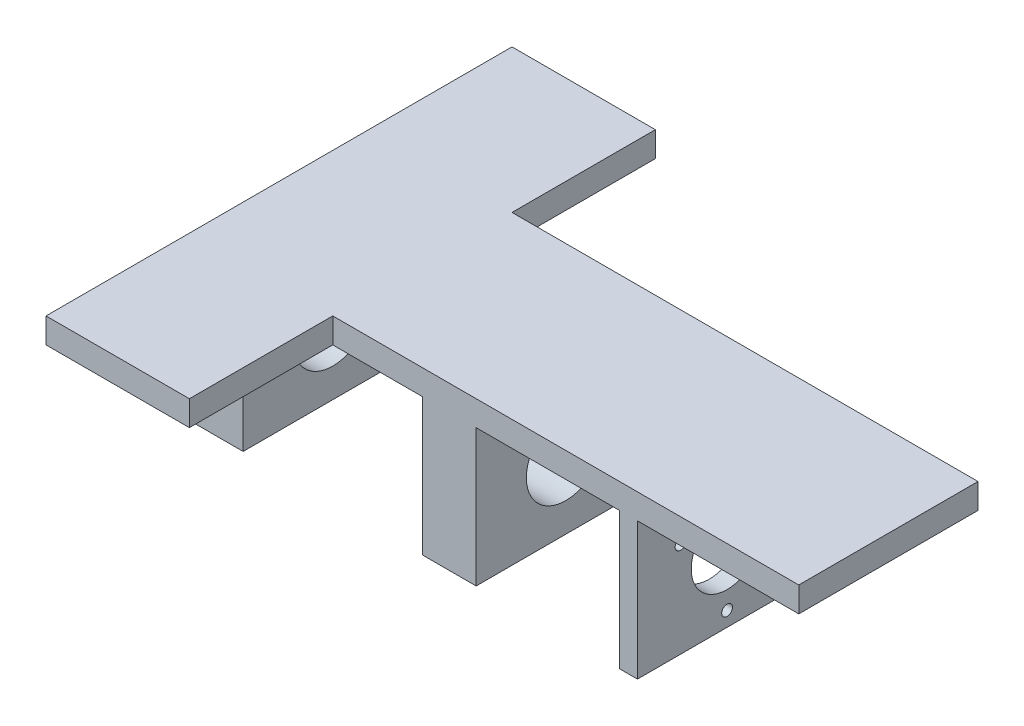
SolidWorks part; units mm, degrees
ref_plane "Front Plane" through (0, 0, 0) normal (0, 0, 1) x (1, 0, 0)
ref_plane "Top Plane" through (0, 0, 0) normal (0, 1, 0) x (1, 0, 0)
ref_plane "Right Plane" through (0, 0, 0) normal (1, 0, 0) x (0, 0, -1)
sketch "Sketch1" plane through (0, 0, 0) normal (0, 1, 0) x (1, 0, 0)
  line L1 (40, 0) -> (170, 0)
  line L2 (0, 0) -> (0, 50)
  line L3 (40, 50) -> (170, 50)
  line L4 (170, 0) -> (170, 50)
  line L5 (0, 90) -> (40, 90)
  line L6 (40, 90) -> (40, 50)
  line L8 (0, 90) -> (0, 50)
  line L9 (0, 0) -> (0, -40)
  line L10 (0, -40) -> (40, -40)
  line L11 (40, -40) -> (40, 0)
  dimension "D1" = 50
  dimension "D2" = 170
  dimension "D3" = 40
  dimension "D4" = 40
  dimension "D5" = 40
  dimension "D6" = 40
  dimension "D7" = 40
  dimension "D8" = 40
extrude "Boss-Extrude2" add sketch "Sketch1" along normal blind 7
sketch "Sketch2" plane through (0, 0, 0) normal (0, -1, 0) x (1, 0, 0)
  line L0 (0, -90) -> (0, 40) construction
  line L2 (170, 0) -> (170, -50) construction
  line L3 (170, -50) -> (40, -50) construction
  line L4 (0, 0) -> (15, 0)
  line L5 (0, 0) -> (0, -50)
  line L6 (0, -50) -> (15, -50)
  line L7 (15, 0) -> (15, -50)
  line L9 (65, 0) -> (80, 0)
  line L10 (65, 0) -> (65, -50)
  line L11 (65, -50) -> (80, -50)
  line L12 (80, 0) -> (80, -50)
  line L26 (120, 0) -> (125, 0)
  line L27 (120, 0) -> (120, -50)
  line L28 (120, -50) -> (125, -50)
  line L29 (125, 0) -> (125, -50)
  dimension "D2" = 50
  dimension "D3" = 15
  dimension "D4" = 50
  dimension "D5" = 0
  dimension "D6" = 50
  dimension "D7" = 15
  dimension "D8" = 40
  dimension "D9" = 170
  dimension "D10" = 50
  dimension "D11" = 5
extrude "Boss-Extrude4" add sketch "Sketch2" along normal blind 38.25
sketch "Sketch10" plane through (0, 0, 0) normal (-1, 0, 0) x (0, 0, 1)
  circle A0 centre (-25, -19.125) radius 11
extrude "Cut-Extrude5" cut sketch "Sketch10" against normal blind 15
sketch "Sketch11" plane through (65, 0, 0) normal (-1, 0, 0) x (0, 0, 1)
  circle A0 centre (-25, -19.125) radius 11
extrude "Cut-Extrude7" cut sketch "Sketch11" against normal blind 15
sketch "Sketch12" plane through (125, 0, 0) normal (1, 0, 0) x (0, 0, -1)
  circle A0 centre (25, -19.125) radius 10
  circle A3 centre (12.0096, -11.625) radius 1.5
  circle A4 centre (37.9904, -11.625) radius 1.5
  circle A5 centre (25, -34.125) radius 1.5
sketch "Sketch23" plane through (125, 0, 0) normal (1, 0, 0) x (0, 0, -1)
  circle A0 centre (25, -19.125) radius 10
  circle A3 centre (12.0096, -11.625) radius 1.5
  circle A4 centre (37.9904, -11.625) radius 1.5
  circle A5 centre (25, -34.125) radius 1.5
extrude "Cut-Extrude10" cut sketch "Sketch23" against normal blind 5
extrude "Cut-Extrude9" cut sketch "Sketch12" against normal blind 5
ref_plane "Plane8" through (200, 7, -50) normal (-1, 0, 0) x (0, 0, 1)
